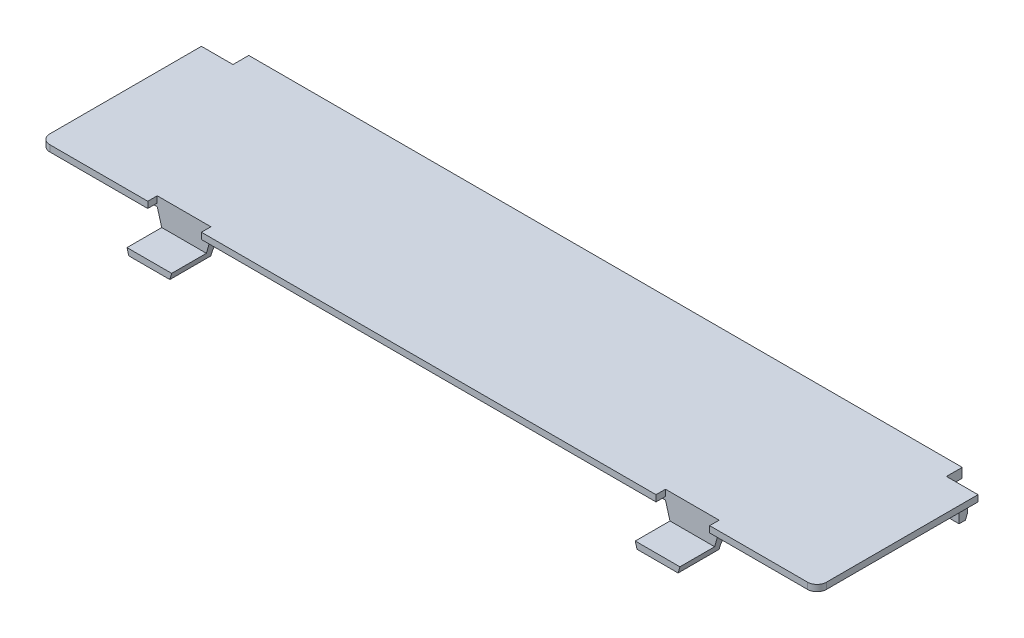
SolidWorks part; units mm, degrees
ref_plane "Front Plane" through (0, 0, 0) normal (0, 0, 1) x (1, 0, 0)
ref_plane "Top Plane" through (0, 0, 0) normal (0, 1, 0) x (1, 0, 0)
ref_plane "Right Plane" through (0, 0, 0) normal (1, 0, 0) x (0, 0, -1)
sketch "Sketch2" plane through (0, 0, 0) normal (0, 1, 0) x (1, 0, 0)
  line L1 (-61.5, 13.25) -> (61.5, 13.25)
  line L2 (-61.5, 13.25) -> (-61.5, -13.25)
  line L3 (-60, -14.75) -> (60, -14.75)
  line L4 (61.5, 13.25) -> (61.5, -13.25)
  line L5 (0, -14.75) -> (0, 13.25) construction
  line L6 (-61.5, 0) -> (61.5, 0) construction
  arc A0 (60, -14.75) -> (61.5, -13.25) centre (60, -13.25) ccw
  arc A1 (-61.5, -13.25) -> (-60, -14.75) centre (-60, -13.25) ccw
  point P7 (61.5, -14.75)
  point P10 (-61.5, -14.75)
  point P44 (0, 0)
  dimension "D3" = 1.5
  dimension "D1" = 123
  dimension "D2" = 28
extrude "Boss-Extrude1" add sketch "Sketch2" along normal blind 1.5
sketch "Sketch9" plane through (0, 0, 0) normal (0, -1, 0) x (1, 0, 0)
  line L4 (61.5, -13.25) -> (-61.5, -13.25) construction
  line L5 (60, -13.25) -> (65, -13.25)
  line L6 (65, -13.25) -> (65, 18.25)
  line L7 (65, 18.25) -> (-65, 18.25)
  line L8 (-60, 13.25) -> (-60, -11.75)
  line L9 (-60, -11.75) -> (60, -11.75)
  line L10 (60, -11.75) -> (60, 13.25)
  line L11 (60, 13.25) -> (-60, 13.25)
  line L12 (-60, 12.45) -> (-60, -13.25)
  line L14 (60, -13.25) -> (60, 12.45)
  line L15 (59.2, 13.25) -> (-59.2, 13.25)
  line L16 (-65, 18.25) -> (-65, -13.25)
  line L17 (-65, -13.25) -> (-60, -13.25)
  arc A2 (-60, 12.45) -> (-59.2, 13.25) centre (-59.2, 12.45) cw
  arc A3 (60, 12.45) -> (59.2, 13.25) centre (59.2, 12.45) ccw
  dimension "D2" = 0.8
  dimension "D3" = 5
  dimension "D4" = 5
  dimension "D5" = 5
  dimension "D1" = 1.5
extrude "Cut-Extrude4" cut sketch "Sketch9" against normal blind 0.5
sketch "Sketch3" plane through (0, 1.5, 0) normal (0, 1, 0) x (1, 0, 0)
  line L0 (-60, -14.75) -> (60, -14.75) construction
  line L1 (-44.5, -12.25) -> (-36, -12.25)
  line L2 (-44.5, -12.25) -> (-44.5, -18.75)
  line L3 (-44.5, -18.75) -> (-36, -18.75)
  line L4 (-36, -12.25) -> (-36, -18.75)
  line L5 (-40.25, -18.75) -> (-40.25, -12.25) construction
  line L6 (-44.5, -15.5) -> (-36, -15.5) construction
  line L7 (-61.5, 13.25) -> (-61.5, -13.25) construction
  point P48 (-40.25, -15.5)
  dimension "D1" = 4
  dimension "D2" = 17
  dimension "D3" = 8.5
  dimension "D4" = 2.5
extrude "Boss-Extrude2" add sketch "Sketch3" against normal blind 5
sketch "Sketch4" plane through (0, 1.5, 0) normal (0, 1, 0) x (1, 0, 0)
  line L0 (-44.5, -14.75) -> (-44.5, -18.75) construction
  line L1 (-44.5, -13.25) -> (-36, -13.25)
  line L2 (-44.5, -13.25) -> (-44.5, -18.75)
  line L3 (-44.5, -18.75) -> (-36, -18.75)
  line L4 (-36, -13.25) -> (-36, -18.75)
  line L5 (-40.25, -18.75) -> (-40.25, -13.25) construction
  line L6 (-44.5, -16) -> (-36, -16) construction
  line L7 (-60, -14.75) -> (-44.5, -14.75) construction
  point P36 (-40.25, -16)
  dimension "D1" = 1.5
extrude "Cut-Extrude1" cut sketch "Sketch4" against normal blind 4
sketch "Sketch5" plane through (0, 0, 18.75) normal (0, 0, 1) x (1, 0, 0)
  line L0 (-44.5, 0) -> (-43.5, -3.5)
  line L1 (-44.5, -3.5) -> (-36, -3.5) construction
  line L2 (-43.5, -3.5) -> (-44.5, -3.5)
  line L3 (-44.5, -3.5) -> (-44.5, 0)
  line L4 (-36, 0) -> (-36, -3.5)
  line L5 (-36, -3.5) -> (-37, -3.5)
  line L6 (-37, -3.5) -> (-36, 0)
  line L7 (-36, 0) -> (59.2, 0) construction
  line L8 (-36, -3.5) -> (-36, -2.5) construction
  dimension "D1" = 1
  dimension "D2" = 1
extrude "Cut-Extrude2" cut sketch "Sketch5" against normal through all
mirror "Mirror1" about plane through (0, 0, 0) normal (1, 0, 0) of "Cut-Extrude2", "Cut-Extrude1", "Boss-Extrude2"
fillet "Fillet1" radius 3 2 edges at (40.25, 0, 12.25) (-40.25, 0, 12.25)
sketch "Sketch6" plane through (0, 1.5, 0) normal (0, 1, 0) x (1, 0, 0)
  line L0 (-61.5, 13.25) -> (-61.5, -13.25) construction
  line L1 (-61.5, 10.75) -> (-56.5, 10.75)
  line L2 (-61.5, 10.75) -> (-61.5, 13.25)
  line L3 (-61.5, 13.25) -> (-56.5, 13.25)
  line L4 (-56.5, 10.75) -> (-56.5, 13.25)
  line L5 (-59, 13.25) -> (-59, 10.75) construction
  line L6 (-61.5, 12) -> (-56.5, 12) construction
  line L7 (61.5, 13.25) -> (-61.5, 13.25) construction
  point P60 (-59, 12)
  dimension "D1" = 5
  dimension "D2" = 2.5
extrude "Cut-Extrude3" cut sketch "Sketch6" against normal up to next (1.5 mm away)
sketch "Sketch7" plane through (-56.5, 0, 0) normal (-1, 0, 0) x (0, 0, 1)
  line L0 (-10.75, 0) -> (-10.75, -0.5)
  line L1 (-10.75, -3) -> (-9.75, -3)
  line L2 (-9.75, -3) -> (-9.75, 0)
  line L3 (-10.75, 0) -> (13.25, 0) construction
  line L4 (-9.75, 0) -> (-10.75, 0)
  line L5 (-10.75, 1.5) -> (13.25, 1.5) construction
  line L6 (-10.75, -3) -> (-11.0476, -2.3)
  line L7 (-10.75, -2.3) -> (-10.75, -3) construction
  line L8 (-10.75, -2.3) -> (-11.0476, -2.3) construction
  line L9 (-10.75, 0) -> (12.45, 0) construction
  line L10 (-10.75, 0) -> (-10.75, 0.5) construction
  arc A1 (-11.0476, -2.3) -> (-10.75, -0.5) centre (-8.6023, -1.7797) cw
  point P15 (-10.75, -3)
  dimension "D4" = 0.7
  dimension "D6" = 2.5
  dimension "D1" = 1
  dimension "D2" = 4.5
  dimension "D3" = 1
  dimension "D5" = 0.2976
  dimension "D7" = 0.5
extrude "Boss-Extrude4" add sketch "Sketch7" along normal blind 3
mirror "Mirror2" about plane through (0, 0, 0) normal (1, 0, 0) of "Boss-Extrude4", "Cut-Extrude3"
sketch "Sketch10" plane through (0, 0, 0) normal (0, -1, 0) x (-1, 0, 0)
  line L0 (-15, 11.5) -> (0, 11.5) construction
  line L1 (0, 11.5) -> (0, 0) construction
  line L2 (-56.5, 13.25) -> (56.5, 13.25) construction
  circle A0 centre (-15, 11.5) radius 1
  circle A1 centre (15, 11.5) radius 1
  dimension "D1" = 2
  dimension "D2" = 15
  dimension "D3" = 1.75
extrude "Boss-Extrude5" add sketch "Sketch10" along normal blind 2.5
fillet "Fillet2" radius 1 2 edges at (58, 0, -9.75) (-58, 0, -9.75)
